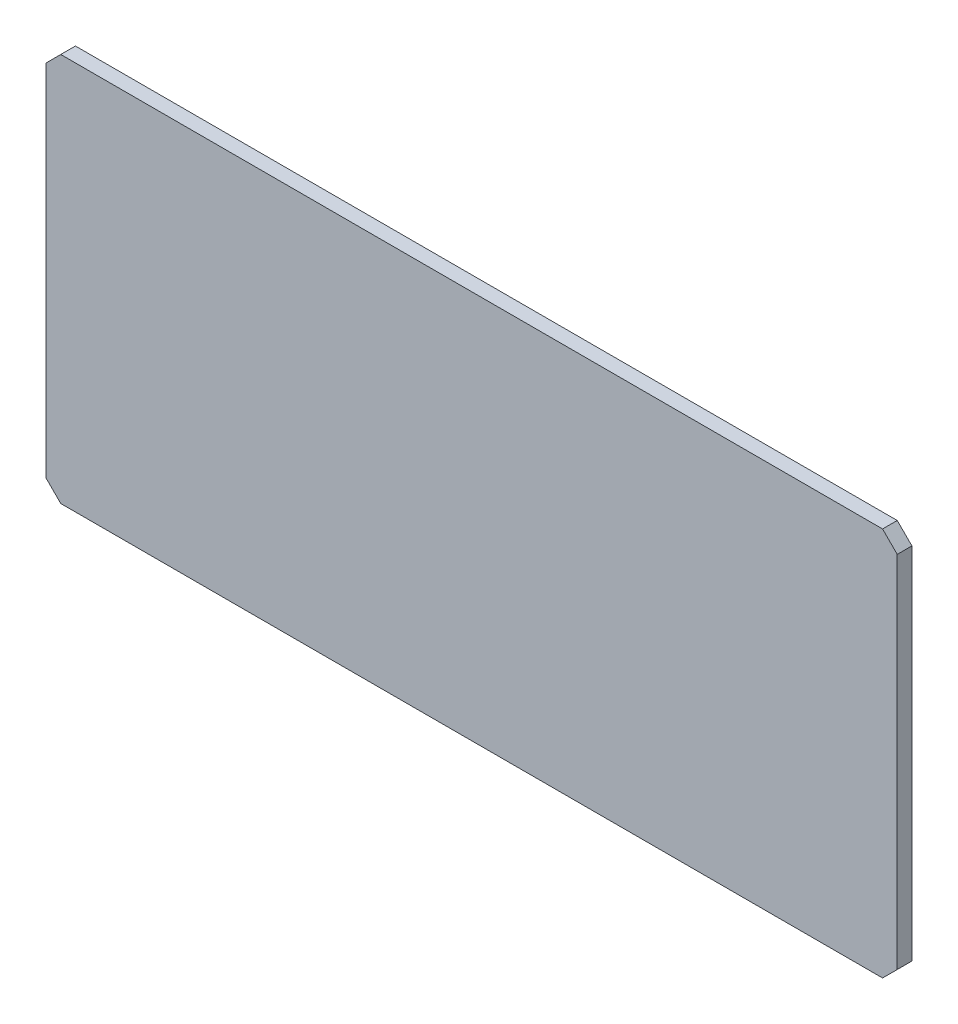
SolidWorks part; units mm, degrees
material "PVC rigide"
ref_plane "Plan de face" through (0, 0, 0) normal (0, 0, 1) x (1, 0, 0)
ref_plane "Plan de dessus" through (0, 0, 0) normal (0, 1, 0) x (1, 0, 0)
ref_plane "Plan de droite" through (0, 0, 0) normal (1, 0, 0) x (0, 0, -1)
sketch "Esquisse1" plane through (0, 0, 0) normal (0, 0, 1) x (1, 0, 0)
  line L1 (0, 0) -> (-116, 0)
  line L2 (0, 0) -> (0, 53)
  line L3 (0, 53) -> (-116, 53)
  line L4 (-116, 0) -> (-116, 53)
  dimension "D1" = 53
  dimension "D2" = 116
extrude "Extrusion1" add sketch "Esquisse1" along normal blind 2
chamfer "Chanfrein1" distance 2 angle 45 4 edges at (0, 0, 1) (-116, 0, 1) (-116, 53, 1) (0, 53, 1)
